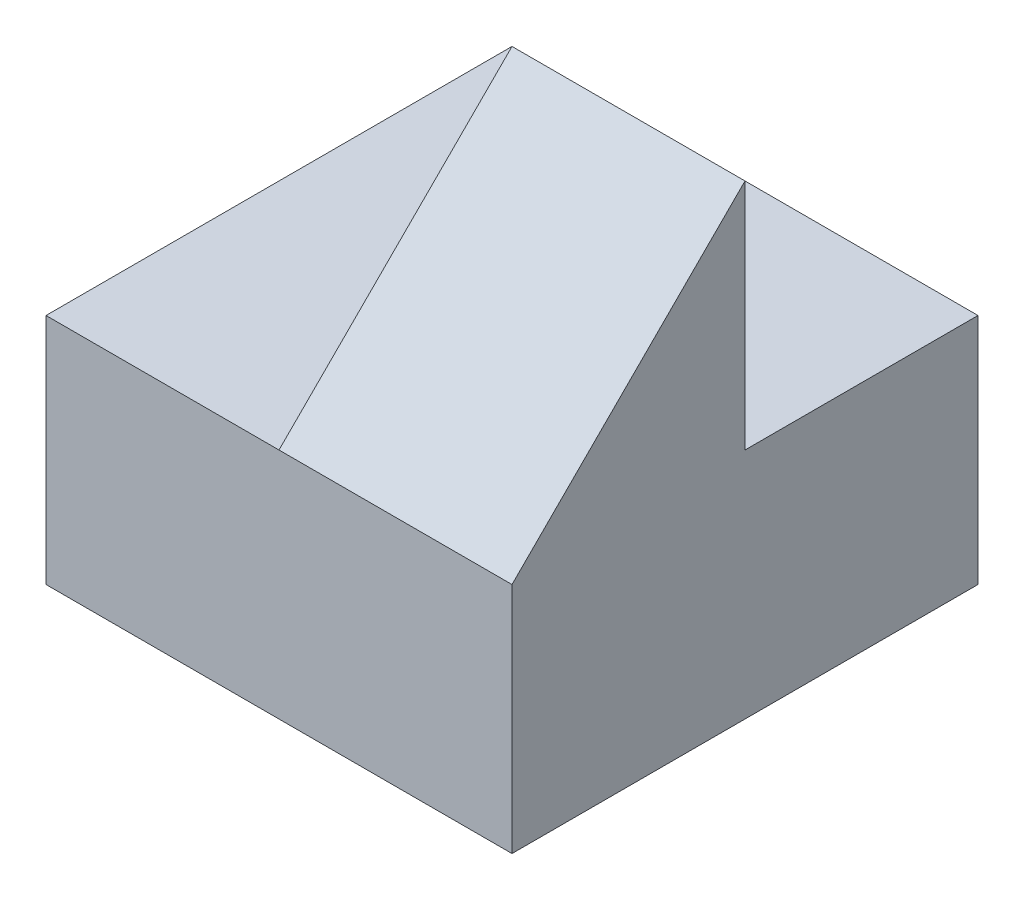
SolidWorks part; units mm, degrees
ref_plane "Front" through (0, 0, 0) normal (0, 0, 1) x (1, 0, 0)
ref_plane "Top" through (0, 0, 0) normal (0, 1, 0) x (1, 0, 0)
ref_plane "Right" through (0, 0, 0) normal (1, 0, 0) x (0, 0, -1)
sketch "Sketch1" plane through (0, 0, 0) normal (0, 1, 0) x (1, 0, 0)
  line L1 (0, 0) -> (4, 0)
  line L2 (0, 0) -> (0, 4)
  line L3 (0, 4) -> (4, 4)
  line L4 (4, 0) -> (4, 4)
  dimension "D1" = 4
  dimension "D2" = 4
extrude "Boss-Extrude1" add sketch "Sketch1" along normal blind 4
sketch "Sketch2" plane through (0, 4, 0) normal (0, 1, 0) x (1, 0, 0)
  line L5 (2, 2) -> (4, 2)
  line L6 (2, 2) -> (2, 0)
  line L7 (2, 0) -> (4, 0)
  line L8 (4, 2) -> (4, 0)
  line M1 (0, 4) -> (0, 0)
  line M2 (0, 0) -> (4, 0)
  line M3 (4, 0) -> (4, 4)
  line M4 (4, 4) -> (0, 4)
  dimension "D1" = 2
  dimension "D2" = 2
  dimension "D3" = 0
extrude "Cut-Extrude1" cut sketch "Sketch2" against normal blind 2 contours L8 L7 M4 M1 M2 M3
sketch "Sketch3" plane through (0, 0, 0) normal (-1, 0, 0) x (0, 0, 1)
  line L0 (-2, 4) -> (0, 2)
  line L2 (0, 2) -> (0, 4)
  line L3 (0, 4) -> (-2, 4)
  point P3 (0, 2)
  point P5 (0, 0)
  point P8 (0, 1)
  point P9 (0, 0)
  point P10 (0, 0)
extrude "Cut-Extrude2" cut sketch "Sketch3" against normal blind 10 contours L2 L3 L0
